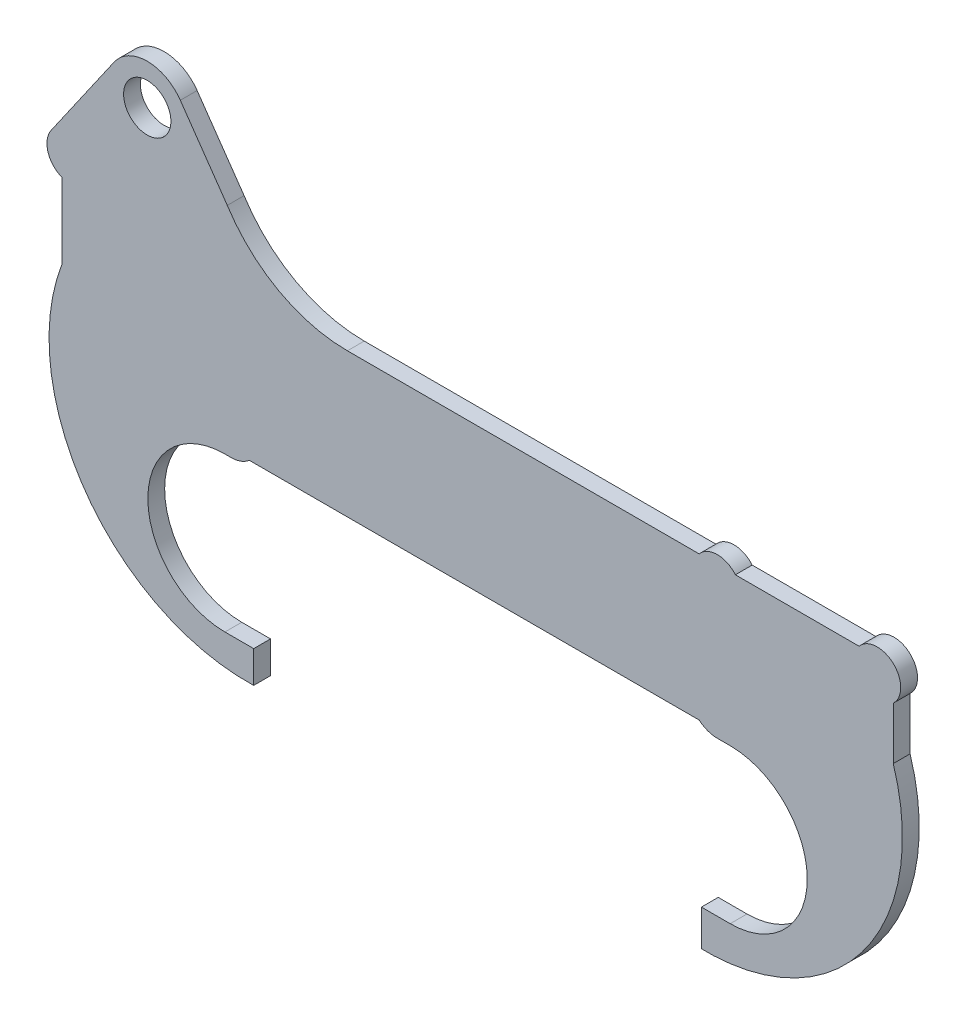
SolidWorks part; units mm, degrees
material "6061-T6 (SS)"
ref_plane "Front Plane" through (0, 0, 0) normal (0, 0, 1) x (1, 0, 0)
ref_plane "Top Plane" through (0, 0, 0) normal (0, 1, 0) x (1, 0, 0)
ref_plane "Right Plane" through (0, 0, 0) normal (1, 0, 0) x (0, 0, -1)
sketch "Sketch1" plane through (0, 0, 0) normal (0, 0, 1) x (1, 0, 0)
  line L0 (-5.08, 71.8936) -> (-5.08, -11.7135) construction
  line L1 (74.4752, 0) -> (253.1086, 0)
  line L2 (0, 30.0884) -> (0, 60.1374)
  line L4 (330.2, 23.5739) -> (330.2, 44.3442)
  line L5 (-50.1663, -2.667) -> (306.9288, -2.667) construction
  line L6 (64.77, -63.881) -> (76.2, -63.881)
  line L7 (73.7489, -76.581) -> (76.2, -76.581)
  line L8 (76.2, -63.881) -> (76.2, -76.581)
  line L9 (64.77, -33.274) -> (265.43, -33.274) construction
  line L10 (335.28, 103.5137) -> (335.28, -21.3902) construction
  line L11 (265.43, -63.881) -> (254, -63.881)
  line L12 (258.8047, -78.1925) -> (254, -78.1925)
  line L13 (254, -63.881) -> (254, -78.1925)
  line L14 (65.7097, 83.3246) -> (47.0585, 110.1402)
  line L15 (-2.1692, 117.0051) -> (128.9663, 117.0051) construction
  line L16 (2.1336, 83.3246) -> (20.7848, 110.1402)
  line L17 (2.1336, 83.3246) -> (-4.236, 74.1668)
  line L18 (265.43, -2.667) -> (260.3119, -2.667)
  line L19 (113.4153, 57.15) -> (253.1297, 57.15)
  line L20 (0, 30.0884) -> (0, 93.6406) construction
  line L21 (264.9982, 57.15) -> (264.9982, 0) construction
  line L22 (255.6256, 60.325) -> (255.6256, 0) construction
  line L23 (260.8297, 60.5151) -> (330.6652, 60.5151) construction
  line L24 (267.4941, 57.15) -> (316.6297, 57.15)
  line L25 (64.77, -2.667) -> (67.2719, -2.667)
  arc A0 (64.77, -2.667) -> (64.77, -63.881) centre (64.77, -33.274) ccw
  arc A1 (0, 30.0884) -> (76.2, -76.5429) centre (73.7489, 2.2479) ccw
  arc A2 (265.43, -63.881) -> (265.43, -2.667) centre (265.43, -33.274) ccw
  arc A3 (47.0585, 110.1402) -> (20.7848, 110.1402) centre (33.9217, 101.0031) ccw
  circle A4 centre (33.9217, 101.0031) radius 9.398
  arc A5 (258.8047, -78.1925) -> (330.2, 23.5739) centre (255.5759, 0) ccw
  arc A6 (-4.236, 74.1668) -> (0, 60.1374) centre (3.4376, 68.8296) ccw
  arc A7 (65.7097, 83.3246) -> (113.4153, 57.15) centre (113.4153, 113.7111) ccw
  arc A8 (267.4941, 57.15) -> (253.1297, 57.15) centre (260.3119, 51.1679) ccw
  arc A9 (330.2, 44.3442) -> (316.6297, 57.15) centre (323.8119, 51.1679) ccw
  arc A10 (67.2719, -2.667) -> (74.4752, 0) centre (67.2719, 8.3943) ccw
  arc A11 (253.1086, 0) -> (260.3119, -2.667) centre (260.3119, 8.3943) ccw
  dimension "D4" = 157.6578
  dimension "D7" = 30.607
  dimension "D11" = 32.004
  dimension "D13" = 18.796
  dimension "D19" = 18.6944
  dimension "D22" = 74.5744
  dimension "D25" = 18.6944
  dimension "D28" = 18.6944
  dimension "D31" = 11.0613
  dimension "D32" = 64.77
  dimension "D5" = 5.08
  dimension "D6" = 2.667
  dimension "D8" = 200.66
  dimension "D9" = 76.2
  dimension "D10" = 5.08
  dimension "D12" = 76.2
  dimension "D14" = 32.6641
  dimension "D15" = 12.7
  dimension "D16" = 32.6641
  dimension "D17" = 2.1336
  dimension "D18" = 69.64
  dimension "D20" = 3.4376
  dimension "D21" = 193.04
  dimension "D23" = 9.3726
  dimension "D24" = 3.3651
  dimension "D26" = 4.6863
  dimension "D27" = 63.5
  dimension "D29" = 57.15
  dimension "D30" = 42.7736
  dimension "D33" = 330.2
  dimension "D34" = 101.0031
extrude "Boss-Extrude1" add sketch "Sketch1" along normal blind 6.6802
